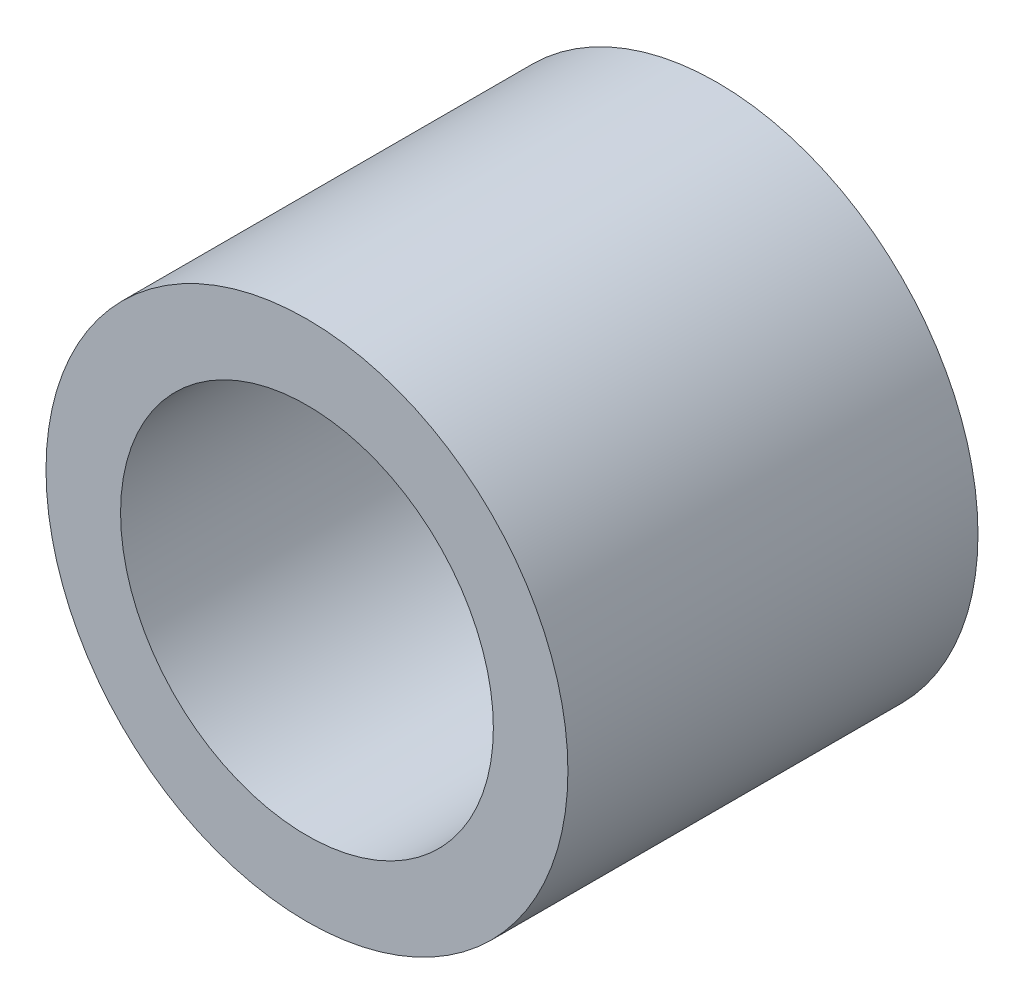
SolidWorks part; units mm, degrees
ref_plane "Plane1" through (0, 0, 0) normal (0, 0, 1) x (1, 0, 0)
ref_plane "Plane2" through (0, 0, 0) normal (0, 1, 0) x (1, 0, 0)
ref_plane "Plane3" through (0, 0, 0) normal (1, 0, 0) x (0, 0, -1)
sketch "Sketch1" plane through (0, 0, 0) normal (0, 0, 1) x (1, 0, 0)
  circle A0 centre (0, 0) radius 7
  circle A1 centre (0, 0) radius 5
  dimension "D1" = 14
  dimension "D2" = 10
extrude "Base-Extrude" add sketch "Sketch1" along normal blind 11
